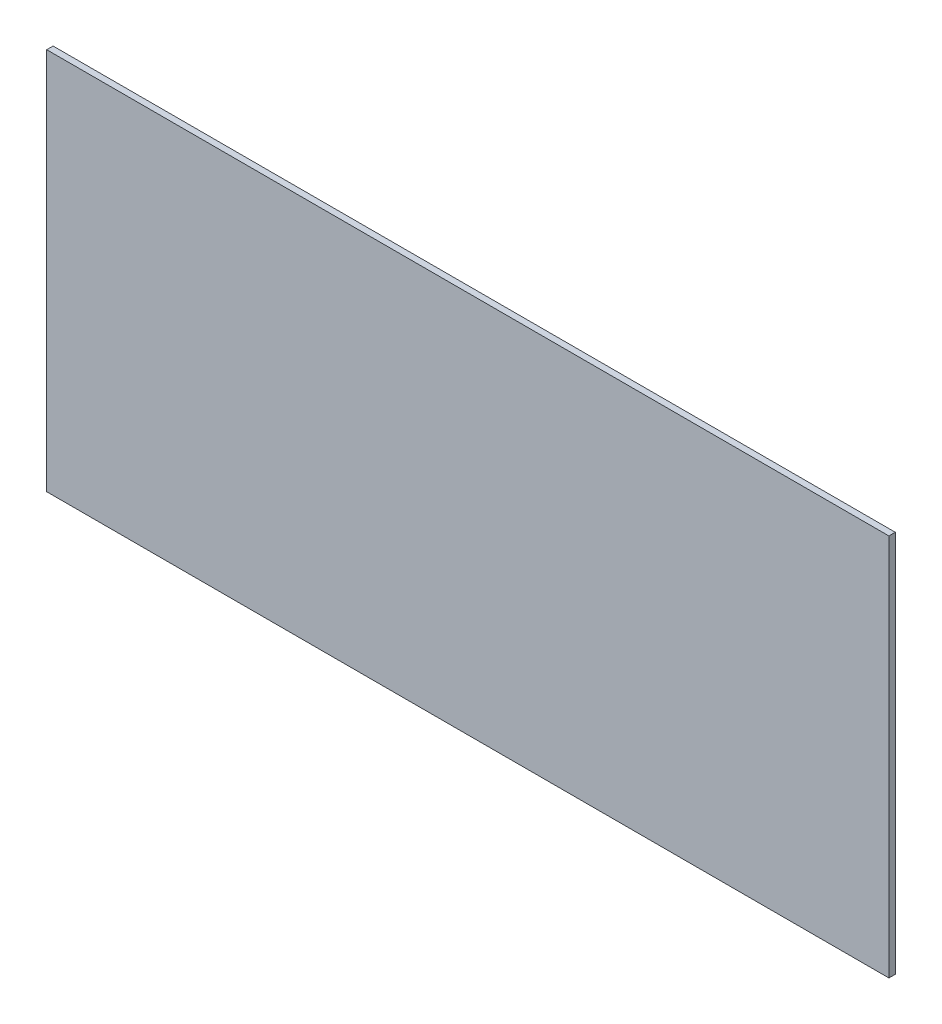
SolidWorks part; units mm, degrees
ref_plane "Front Plane" through (0, 0, 0) normal (0, 0, 1) x (1, 0, 0)
ref_plane "Top Plane" through (0, 0, 0) normal (0, 1, 0) x (1, 0, 0)
ref_plane "Right Plane" through (0, 0, 0) normal (1, 0, 0) x (0, 0, -1)
sketch "Sketch1" plane through (0, 0, 0) normal (0, 0, 1) x (1, 0, 0)
  line L1 (-74.1235, 46.0212) -> (57.8765, 46.0212)
  line L2 (-74.1235, 46.0212) -> (-74.1235, -13.9788)
  line L3 (-74.1235, -13.9788) -> (57.8765, -13.9788)
  line L4 (57.8765, 46.0212) -> (57.8765, -13.9788)
  dimension "D1" = 132
  dimension "D2" = 60
extrude "Boss-Extrude1" add sketch "Sketch1" along normal blind 1
